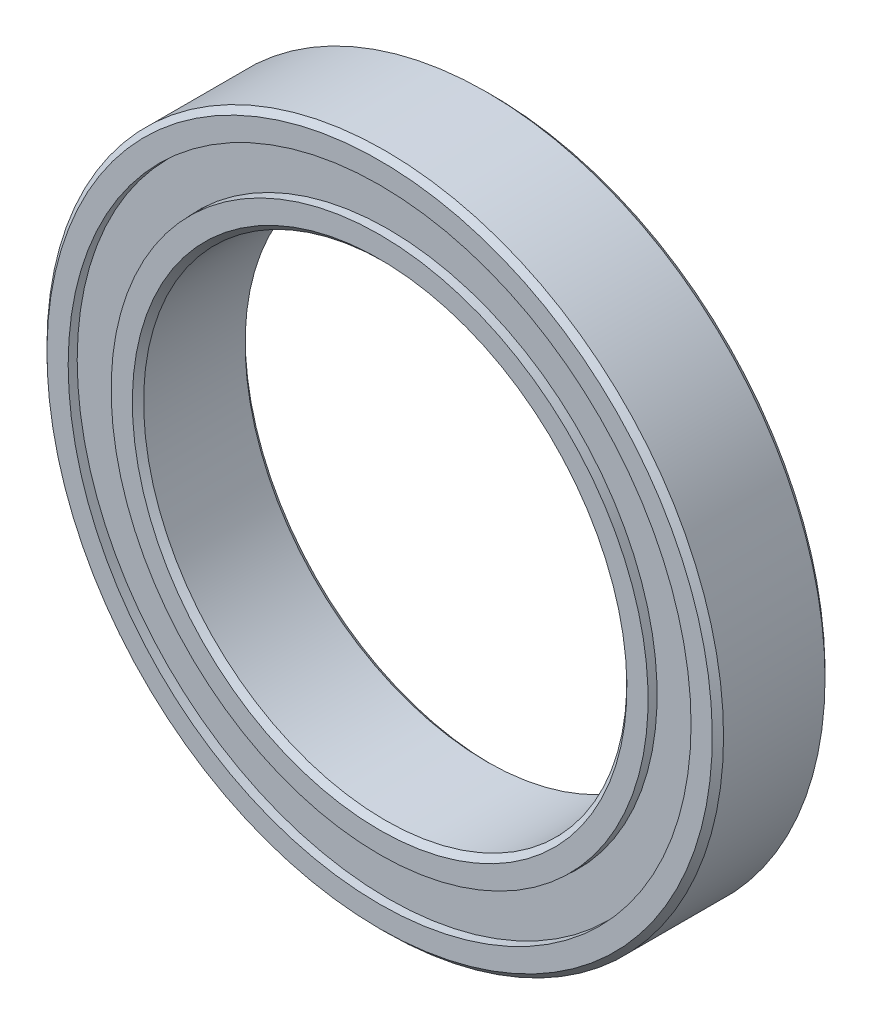
SolidWorks part; units mm, degrees
ref_plane "Front Plane" through (0, 0, 0) normal (0, 0, 1) x (1, 0, 0)
ref_plane "Top Plane" through (0, 0, 0) normal (0, 1, 0) x (1, 0, 0)
ref_plane "Right Plane" through (0, 0, 0) normal (1, 0, 0) x (0, 0, -1)
sketch "Sketch1" plane through (0, 0, 0) normal (0, 0, 1) x (1, 0, 0)
  circle A0 centre (0, 0) radius 21
  circle A1 centre (0, 0) radius 15
  dimension "OD" = 42
  dimension "ID" = 30
sketch "Sketch8" plane through (0, 0, 0) normal (1, 0, 0) x (0, 0, -1)
  line L1 (-3.5, 21) -> (3.5, 21)
  line L2 (-3.5, 21) -> (-3.5, -21)
  line L3 (-3.5, -21) -> (3.5, -21)
  line L4 (3.5, 21) -> (3.5, -21)
  line L5 (-3.5, 21) -> (3.5, -21) construction
  line L6 (-3.5, -21) -> (3.5, 21) construction
  point P0 (0, 0)
  point P6 (0, -21)
  dimension "Width" = 7
sketch "Sketch5" plane through (0, 0, 0) normal (1, 0, 0) x (0, 0, -1)
  line L0 (-3.5, 0) -> (3.5, 0) construction
  line L1 (0, 21) -> (0, -21) construction
  line L2 (3.15, 21) -> (-3.15, 21)
  line L3 (-3.15, 21) -> (-3.5, 20.65)
  line L4 (-3.5, 20.65) -> (-3.5, 19.3333)
  line L5 (-3.5, 19.3333) -> (-1.5556, 19.3333)
  line L6 (3.5, 19.3333) -> (1.5556, 19.3333)
  line L7 (3.5, 20.65) -> (3.5, 19.3333)
  line L8 (3.15, 21) -> (3.5, 20.65)
  line L9 (0, 21) -> (0, 18) construction
  line L10 (0, 18) -> (0, 15) construction
  line L11 (-2.0488, 18) -> (-3.5, 18) construction
  line L12 (2.5839, 16.6921) -> (2.9649, 16.6921)
  line L13 (-2.5839, 16.6921) -> (-2.9649, 16.6921)
  line L14 (-2.5839, 16.6921) -> (-2.5839, 19.3079)
  line L15 (-2.5839, 19.3079) -> (-2.9649, 19.3079)
  line L16 (-2.9649, 16.6921) -> (-2.9649, 19.3079)
  line L17 (-2.5839, 16.6921) -> (-2.9649, 19.3079) construction
  line L18 (-2.5839, 19.3079) -> (-2.9649, 16.6921) construction
  line L19 (2.9649, 16.6921) -> (2.9649, 19.3079)
  line L20 (2.5839, 19.3079) -> (2.9649, 19.3079)
  line L21 (2.5839, 16.6921) -> (2.5839, 19.3079)
  line L22 (0, 21) -> (0, -21) construction
  line L23 (3.5, 0) -> (3.5, 21) construction
  line L24 (3.5, 21) -> (3.15, 21) construction
  line L25 (-3.5, 0) -> (-3.5, 21) construction
  line L26 (-3.5, 21) -> (-3.15, 21) construction
  line L27 (3.5, 0) -> (3.5, -21) construction
  line L28 (-3.5, 0) -> (-3.5, -21) construction
  line L29 (-3.5, -21) -> (3.5, -21) construction
  arc A0 (-1.5556, 19.3333) -> (1.5556, 19.3333) centre (0, 18) cw
  circle A1 centre (0, 18) radius 2.0488 construction
  point P14 (0, 15)
  point P15 (-2.7744, 18)
  dimension "D1" = 45
  dimension "D2" = 0.35
  dimension "D3" = 3.1111
  dimension "D4" = 1.3333
  dimension "D5" = 0.381
  dimension "D6" = 0.0254
revolve "Revolve1" add sketch "Sketch5" angle 360 about L0
sketch "Sketch3" plane through (0, 0, 0) normal (1, 0, 0) x (0, 0, -1)
  line L0 (-3.5, 16.6667) -> (-1.5556, 16.6667)
  line L1 (0, 21) -> (0, -21) construction
  line L2 (-3.5, 20.65) -> (-3.5, 19.3333) construction
  line L3 (-3.5, 16.6667) -> (-3.5, 15.35)
  line L4 (-3.15, 21) -> (-3.5, 20.65) construction
  line L5 (-3.5, 15.35) -> (-3.15, 15)
  line L6 (-3.15, 15) -> (3.15, 15)
  line L7 (3.15, 21) -> (3.15, -21) construction
  line L8 (3.15, 15) -> (3.5, 15.35)
  line L9 (3.5, -20.65) -> (3.5, 20.65) construction
  line L10 (3.5, 15.35) -> (3.5, 16.6667)
  line L11 (3.5, 16.6667) -> (1.5556, 16.6667)
  line L13 (3.15, 21) -> (3.5, 20.65) construction
  arc A0 (1.5556, 19.3333) -> (-1.5556, 19.3333) centre (0, 18) ccw construction
  arc A1 (1.5556, 16.6667) -> (-1.5556, 16.6667) centre (0, 18) cw
revolve "Revolve3" add sketch "Sketch3" angle 360 about L0
sketch "Sketch4" plane through (0, 0, 0) normal (1, 0, 0) x (0, 0, -1)
  line L0 (-2.0488, 18) -> (2.0488, 18)
  arc A2 (-2.0488, 18) -> (2.0488, 18) centre (0, 18) cw
  arc A3 (1.5556, 19.3333) -> (-1.5556, 19.3333) centre (0, 18) ccw construction
revolve "Revolve4" add sketch "Sketch4" angle 360 about L0
pattern_circular "CirPattern1" count 17 every 21.176 about axis through (0, 0, 0) along (0, 0, 1) of bodies 104
equation "\"D2@Sketch5\" = \"Width@Sketch8\" * .05"
equation "\"D3@Sketch5\" = \"Width@Sketch8\" / 2.25"
equation "\"D4@Sketch5\"=((\"OD@Sketch1\"-\"ID@Sketch1\")/2)/4.5"
equation "\"D2@CirPattern1\" = 360/\"Balls@CirPattern1\""
